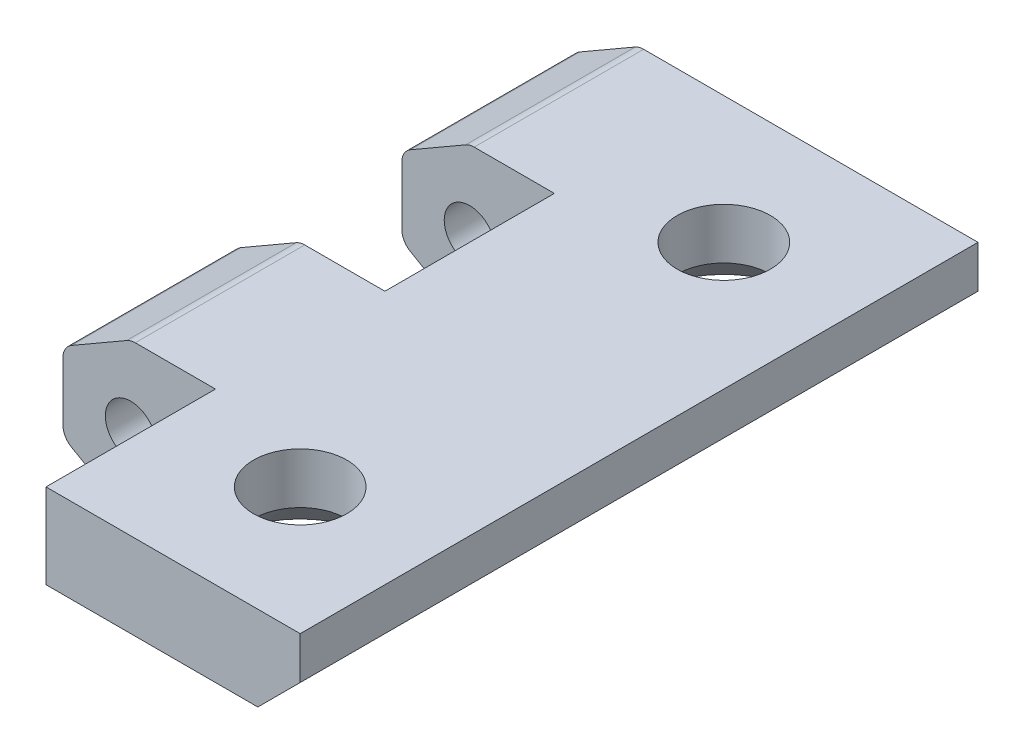
SolidWorks part; units mm, degrees
ref_plane "前视基准面" through (0, 0, 0) normal (0, 0, 1) x (1, 0, 0)
ref_plane "上视基准面" through (0, 0, 0) normal (0, 1, 0) x (1, 0, 0)
ref_plane "右视基准面" through (0, 0, 0) normal (1, 0, 0) x (0, 0, -1)
sketch "Sketch1" plane through (0, 0, 0) normal (0, 0, 1) x (1, 0, 0)
  line L0 (17.5, -0.3812) -> (20, 2.1188)
  line L1 (4, -2.3094) -> (4, -0.3812)
  line L3 (0, 4.6188) -> (-4, 2.3094)
  line L4 (-4, 2.3094) -> (-4, -2.3094)
  line L5 (-4, -2.3094) -> (0, -4.6188)
  line L6 (0, -4.6188) -> (4, -2.3094)
  line L7 (0, 4.6188) -> (20, 4.6188)
  line L9 (3.9818, -0.3812) -> (17.5, -0.3812)
  line L10 (20, 4.6188) -> (20, 2.1188)
  line L11 (2, 3.4641) -> (0, 4.6188) [skipped]
  circle A0 centre (0, 0) radius 4 construction
  circle A1 centre (0, 0) radius 1.5
  point P1 (20, -0.3812)
  dimension "D4" = 3
  dimension "D1" = 5
  dimension "D2" = 8
  dimension "D3" = 20
extrude "Extrude1" add sketch "Sketch1" along normal blind 40
sketch "Sketch2" plane through (0, -0.3812, 0) normal (0, -1, 0) x (1, 0, 0)
  line L0 (0, 40) -> (0, 0) construction
  line L1 (0, 32.5) -> (12.5, 32.5) construction
  line L2 (0, 32.5) -> (0, 7.5) construction
  line L3 (0, 7.5) -> (12.5, 7.5) construction
  line L4 (12.5, 32.5) -> (12.5, 7.5) construction
  line L5 (4, 40) -> (17.5, 40) construction
  circle A0 centre (12.5, 32.5) radius 2.75
  circle A1 centre (12.5, 7.5) radius 2.75
  dimension "D4" = 5.5
  dimension "D1" = 12.5
  dimension "D2" = 25
  dimension "D3" = 7.5
extrude "Extrude2" cut sketch "Sketch2" against normal blind 10
chamfer "Chamfer1" distance 2 angle 45 2 edges at (12.5, -0.3812, 4.75) (12.5, -0.3812, 29.75)
sketch "Sketch3" plane through (0, 4.6188, 0) normal (0, 1, 0) x (1, 0, 0)
  line L0 (0, -40) -> (20, -40) construction
  line L1 (5, -40) -> (-7.7336, -40)
  line L2 (5, -40) -> (5, -30)
  line L3 (5, -30) -> (-7.7336, -30)
  line L4 (-7.7336, -40) -> (-7.7336, -30)
  line L5 (-4, -40) -> (-4, 0) construction
  line L6 (5, -20) -> (-8.3995, -20)
  line L7 (5, -20) -> (5, -10)
  line L8 (5, -10) -> (-8.3995, -10)
  line L9 (-8.3995, -20) -> (-8.3995, -10)
  dimension "D1" = 10
  dimension "D2" = 10
  dimension "D3" = 10
  dimension "D4" = 9
extrude "Extrude3" cut sketch "Sketch3" against normal blind 10
fillet "Fillet1" radius 1 10 edges at (0, 4.6188, 25) (0, 4.6188, 5) (-4, 2.3094, 25) (-4, 2.3094, 5) (-4, -2.3094, 5) (-4, -2.3094, 25) (0, -4.6188, 5) (0, -4.6188, 25) (4, -2.3094, 25) (4, -2.3094, 5)
